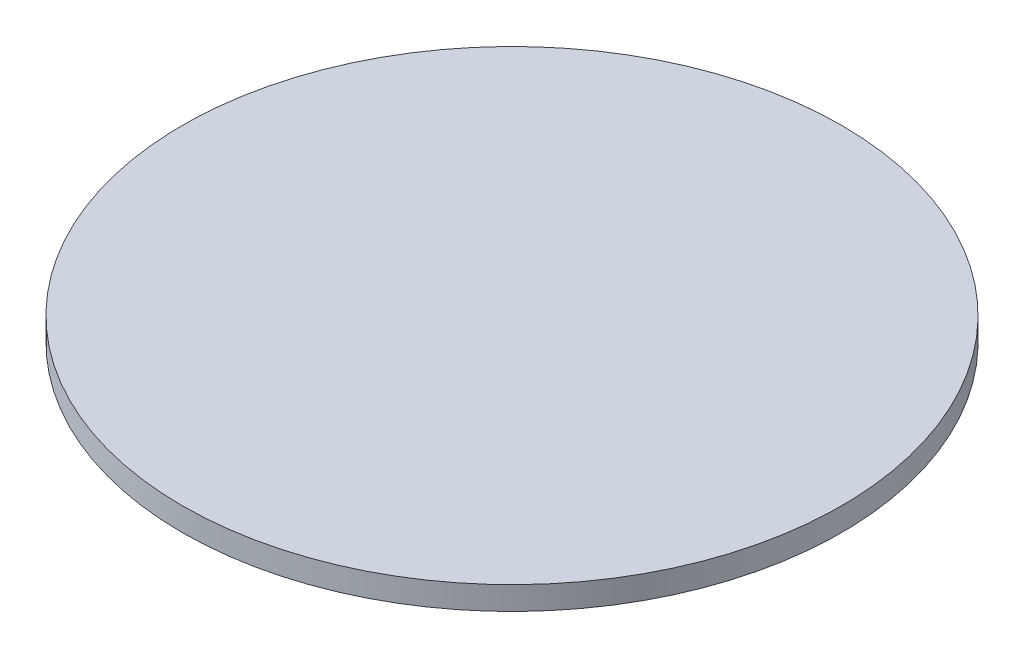
SolidWorks part; units mm, degrees
ref_plane "Front Plane" through (0, 0, 0) normal (0, 0, 1) x (1, 0, 0)
ref_plane "Top Plane" through (0, 0, 0) normal (0, 1, 0) x (1, 0, 0)
ref_plane "Right Plane" through (0, 0, 0) normal (1, 0, 0) x (0, 0, -1)
sketch "Sketch1" plane through (0, 0, 0) normal (0, 1, 0) x (1, 0, 0)
  circle A0 centre (0, 0) radius 45
  dimension "D1" = 90
extrude "Boss-Extrude1" add sketch "Sketch1" along normal blind 3.175
